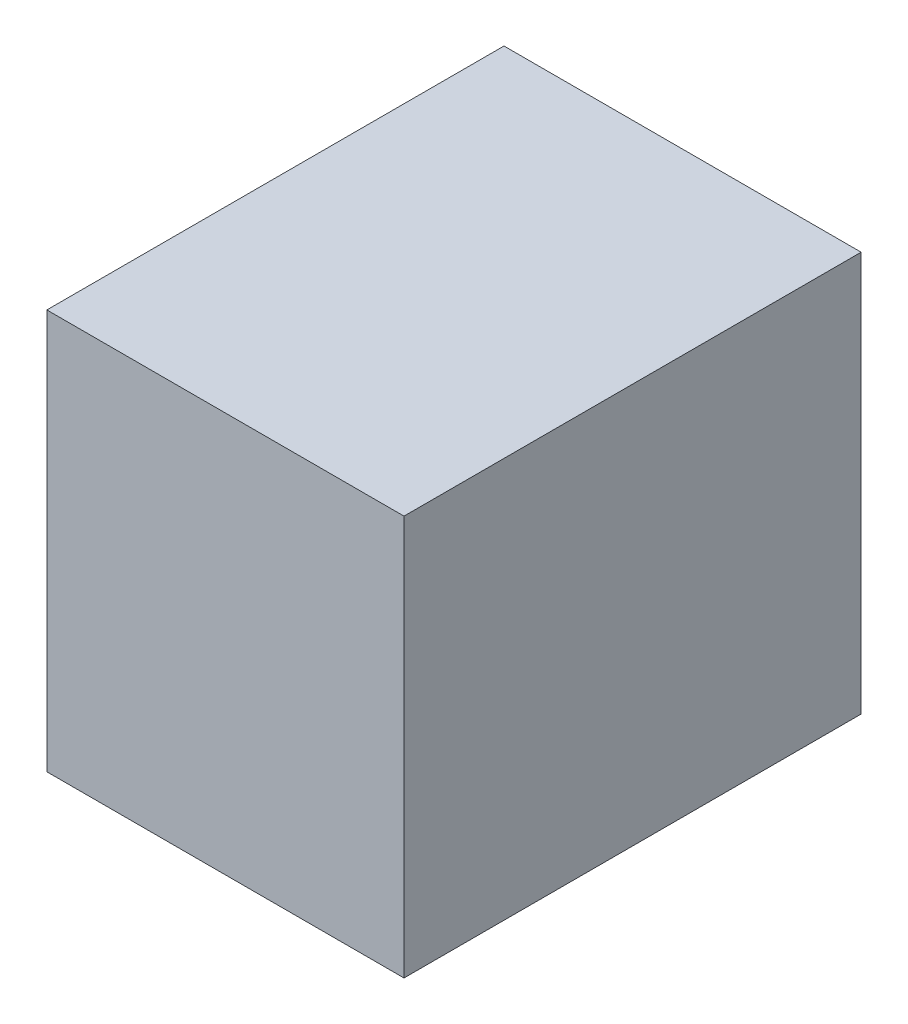
SolidWorks part; units mm, degrees
ref_plane "Front Plane" through (0, 0, 0) normal (0, 0, 1) x (1, 0, 0)
ref_plane "Top Plane" through (0, 0, 0) normal (0, 1, 0) x (1, 0, 0)
ref_plane "Right Plane" through (0, 0, 0) normal (1, 0, 0) x (0, 0, -1)
sketch "Sketch1" plane through (0, 0, 0) normal (1, 0, 0) x (0, 0, -1)
  line L1 (-160, 140) -> (160, 140)
  line L2 (-160, 140) -> (-160, -140)
  line L3 (-160, -140) -> (160, -140)
  line L4 (160, 140) -> (160, -140)
  line L5 (-160, 140) -> (160, -140) construction
  line L6 (-160, -140) -> (160, 140) construction
  point P0 (0, 0)
  dimension "D1" = 320
  dimension "D2" = 280
extrude "Boss-Extrude1" add sketch "Sketch1" along normal blind 250
